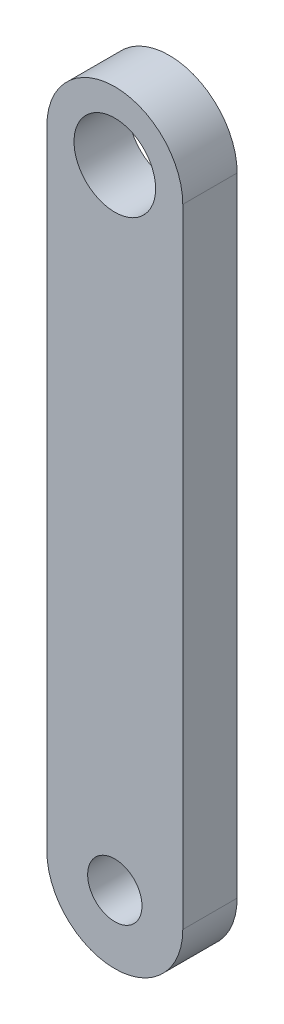
SolidWorks part; units mm, degrees
ref_plane "Front Plane" through (0, 0, 0) normal (0, 0, 1) x (1, 0, 0)
ref_plane "Top Plane" through (0, 0, 0) normal (0, 1, 0) x (1, 0, 0)
ref_plane "Right Plane" through (0, 0, 0) normal (1, 0, 0) x (0, 0, -1)
sketch "Sketch1" plane through (0, 0, 0) normal (0, 0, 1) x (1, 0, 0)
  line L0 (0, 5.7747) -> (0, -5.7747) construction
  line L1 (-1.25, 5.7747) -> (-1.25, -5.7747)
  line L2 (1.25, 5.7747) -> (1.25, -5.7747)
  circle A0 centre (0, 5.7747) radius 0.75
  arc A1 (1.25, 5.7747) -> (-1.25, 5.7747) centre (0, 5.7747) ccw
  arc A2 (1.25, -5.7747) -> (-1.25, -5.7747) centre (0, -5.7747) cw
  circle A3 centre (0, -5.7747) radius 0.5
  dimension "D2" = 1.5
  dimension "D3" = 2.5
  dimension "D4" = 1
  dimension "D1" = 11.5494
extrude "Boss-Extrude1" add sketch "Sketch1" along normal blind 1
